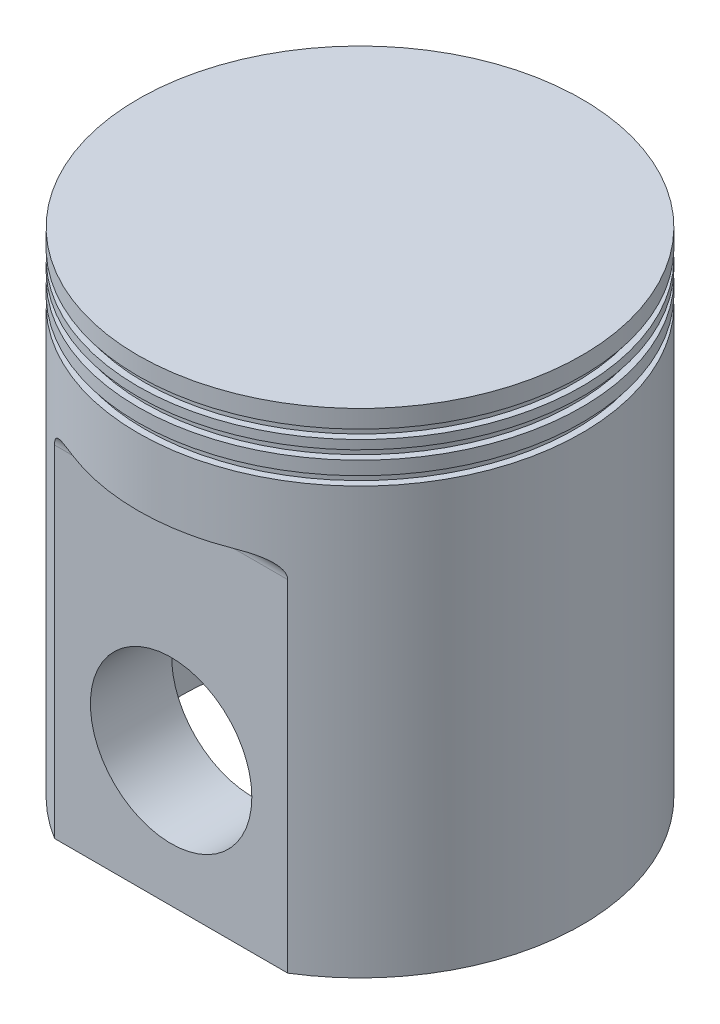
SolidWorks part; units mm, degrees
ref_plane "Přední rovina" through (0, 0, 0) normal (0, 0, 1) x (1, 0, 0)
ref_plane "Horní rovina" through (0, 0, 0) normal (0, 1, 0) x (1, 0, 0)
ref_plane "Pravá rovina" through (0, 0, 0) normal (1, 0, 0) x (0, 0, -1)
sketch "Skica2" plane through (0, 0, 0) normal (0, 0, 1) x (1, 0, 0)
  line L0 (0, 49.5518) -> (0, -37.5109) construction
  line L1 (0, 0) -> (24.75, 0)
  line L2 (24.75, 0) -> (24.75, 47.5)
  line L3 (24.75, 47.5) -> (24, 47.5)
  line L4 (24, 47.5) -> (24, 48.5)
  line L5 (24, 48.5) -> (24.75, 48.5)
  line L6 (24.75, 48.5) -> (24.75, 50)
  line L7 (24.75, 50) -> (24, 50)
  line L8 (24, 50) -> (24, 51)
  line L9 (24, 51) -> (24.75, 51)
  line L10 (24.75, 51) -> (24.75, 52)
  line L11 (24.75, 52) -> (24, 52)
  line L12 (24, 52) -> (24, 53)
  line L13 (24, 53) -> (24.75, 53)
  line L14 (24.75, 53) -> (24.75, 55)
  line L15 (24.75, 55) -> (0, 55)
  line L16 (0, 55) -> (0, 0)
  dimension "D1" = 49.5
  dimension "D2" = 1
  dimension "D3" = 1
  dimension "D4" = 1
  dimension "D5" = 48
  dimension "D6" = 2
  dimension "D7" = 1
  dimension "D8" = 1.5
  dimension "D9" = 55
revolve "Rotovat1" add sketch "Skica2" angle 360 about L0
sketch "Skica3" plane through (0, 0, 0) normal (0, 0, 1) x (1, 0, 0)
  circle A0 centre (0, 15) radius 9
  dimension "D1" = 18
  dimension "D2" = 15
extrude "Odebrat vysunutím1" cut sketch "Skica3" against normal through all and the other way through all
sketch "Skica4" plane through (0, 0, 0) normal (0, -1, 0) x (1, 0, 0)
  line L0 (13, 21.0609) -> (-13, 21.0609)
  line L1 (-13, -21.0609) -> (13, -21.0609)
  line L2 (-15.6864, -12) -> (15.6864, -12)
  line L4 (15.6864, 12) -> (-15.6864, 12)
  circle A0 centre (0, 0) radius 19.75 construction
  circle A1 centre (0, 0) radius 24.75
  circle A2 centre (0, 0) radius 24.75
  arc A3 (-15.6864, -12) -> (-15.6864, 12) centre (0, 0) cw
  arc A4 (15.6864, 12) -> (15.6864, -12) centre (0, 0) cw
  circle M6 centre (0, 0) radius 24.75
  dimension "D3" = 5
  dimension "D2" = 26
  dimension "D4" = 24
  dimension "D1" = 0
extrude "Odebrat vysunutím2" cut sketch "Skica4" against normal blind 40 contours L0 M6 | A4 L4 A3 L2 | L1 M6
fillet "Zaoblit1" radius 2 6 edges at (0, 40, -12) (-19.75, 40, 0) (0, 40, 12) (19.75, 40, 0) (0, 40, 21.0609) (0, 40, -21.0609)
